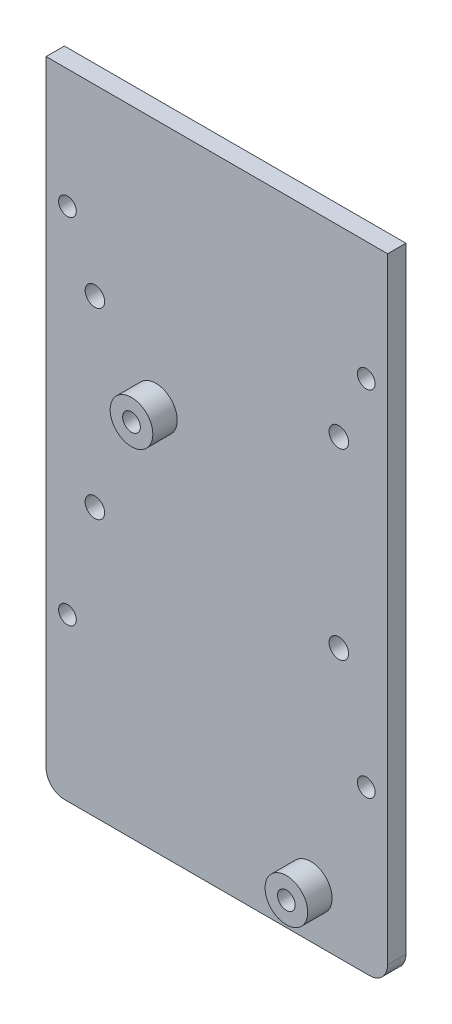
SolidWorks part; units mm, degrees
material "ABS"
ref_plane "Front Plane" through (0, 0, 0) normal (0, 0, 1) x (1, 0, 0)
ref_plane "Top Plane" through (0, 0, 0) normal (0, 1, 0) x (1, 0, 0)
ref_plane "Right Plane" through (0, 0, 0) normal (1, 0, 0) x (0, 0, -1)
sketch "Sketch2" plane through (0, 0, 0) normal (0, 0, 1) x (1, 0, 0)
  line L0 (-15.1668, -33.2317) -> (-15.1668, -38.1317) construction
  line L1 (-15.1668, -33.2317) -> (-2.5668, -33.2317) construction
  line L2 (-40.5668, 21.9683) -> (-40.5668, -38.1317) construction
  line L3 (-40.5668, 21.9683) -> (-2.5668, 21.9683) construction
  line L4 (-55.5668, -38.1317) -> (-5.5668, -38.1317)
  line L5 (-2.5668, -35.1317) -> (-2.5668, 65.8683)
  line L6 (-58.5668, 65.8683) -> (-58.5668, -35.1317)
  line L7 (-55.5668, -38.1317) -> (-5.5668, -38.1317) construction
  line L8 (-2.5668, -35.1317) -> (-2.5668, 65.8683) construction
  line L9 (-2.5668, 65.8683) -> (-58.5668, 65.8683)
  line L10 (-58.5668, 65.8683) -> (-58.5668, -35.1317) construction
  line L11 (-30.5668, -38.1317) -> (-30.5668, 46.8683) construction
  line L12 (-58.5668, 46.8683) -> (-2.5668, 46.8683) construction
  line L13 (-30.5668, 65.8683) -> (-30.5668, 10.8683) construction
  line L14 (-30.5668, 10.8683) -> (-2.5668, 10.8683) construction
  arc A1 (-5.5668, -38.1317) -> (-2.5668, -35.1317) centre (-5.5668, -35.1317) ccw
  arc A2 (-58.5668, -35.1317) -> (-55.5668, -38.1317) centre (-55.5668, -35.1317) ccw
  circle A3 centre (-15.1668, -33.2317) radius 1.25 construction
  circle A4 centre (-40.5668, 21.9683) radius 1.25 construction
  arc A5 (-5.5668, -38.1317) -> (-2.5668, -35.1317) centre (-5.5668, -35.1317) ccw construction
  arc A6 (-58.5668, -35.1317) -> (-55.5668, -38.1317) centre (-55.5668, -35.1317) ccw construction
extrude "Boss-Extrude1" add sketch "Sketch2" along normal blind 3
sketch "Sketch3" plane through (0, 0, 3) normal (0, 0, 1) x (1, 0, 0)
  line L0 (-30.5668, 65.8683) -> (-50.5668, 65.8683) construction
  line L1 (-2.5668, 65.8683) -> (-58.5668, 65.8683) construction
  line L2 (-50.5668, 65.8683) -> (-50.5668, 35.8683) construction
  line L3 (-2.5668, 47.3683) -> (-2.5668, 43.8683) construction
  line L4 (-50.5668, 35.8683) -> (-50.5668, 5.8683) construction
  line L5 (-30.5668, 65.8683) -> (-30.5668, 46.8683) construction
  line L7 (-2.5668, 43.8683) -> (-6.0668, 43.8683) construction
  line L8 (-6.0668, 43.8683) -> (-6.0668, -14.1317) construction
  line L9 (-6.0668, -14.1317) -> (-6.0668, -37.6317) construction
  line L11 (-55.0668, 46.3683) -> (-58.5668, 46.3683) construction
  line L12 (-58.5668, 65.8683) -> (-58.5668, -35.1317) construction
  line L13 (-55.0668, -11.6317) -> (-58.5668, -11.6317) construction
  circle A0 centre (-50.5668, 35.8683) radius 1.6
  circle A1 centre (-50.5668, 5.8683) radius 1.6
  circle A2 centre (-10.5668, 5.8683) radius 1.6
  circle A3 centre (-10.5668, 35.8683) radius 1.6
  circle A4 centre (-40.5668, 24.9683) radius 1.45
  circle A5 centre (-15.1668, -30.2317) radius 1.45
  circle A6 centre (-6.0668, 46.3683) radius 1.45
  circle A7 centre (-6.0668, -11.6317) radius 1.45
  circle A8 centre (-55.0668, -11.6317) radius 1.45
  circle A9 centre (-55.0668, 46.3683) radius 1.45
extrude "Cut-Extrude1" cut sketch "Sketch3" against normal through all
sketch "Sketch4" plane through (0, 0, 3) normal (0, 0, 1) x (1, 0, 0)
  line L4 (-55.5668, -38.1317) -> (-5.5668, -38.1317)
  line L5 (-2.5668, -35.1317) -> (-2.5668, 65.8683)
  line L6 (-2.5668, 65.8683) -> (-58.5668, 65.8683)
  line L7 (-58.5668, 65.8683) -> (-58.5668, -35.1317)
  line L8 (-55.5668, -38.1317) -> (-5.5668, -38.1317)
  line L9 (-2.5668, -35.1317) -> (-2.5668, 65.8683)
  line L10 (-2.5668, 65.8683) -> (-58.5668, 65.8683)
  line L11 (-58.5668, 65.8683) -> (-58.5668, -35.1317)
  circle A0 centre (-55.0668, 46.3683) radius 1.45 construction
  circle A1 centre (-55.0668, -11.6317) radius 1.45 construction
  arc A2 (-58.5668, -35.1317) -> (-55.5668, -38.1317) centre (-55.5668, -35.1317) ccw
  arc A3 (-5.5668, -38.1317) -> (-2.5668, -35.1317) centre (-5.5668, -35.1317) ccw
  arc A4 (-58.5668, -35.1317) -> (-55.5668, -38.1317) centre (-55.5668, -35.1317) ccw
  arc A5 (-5.5668, -38.1317) -> (-2.5668, -35.1317) centre (-5.5668, -35.1317) ccw
  circle A6 centre (-6.0668, 46.3683) radius 1.45 construction
  circle A8 centre (-6.0668, -11.6317) radius 1.45 construction
  circle A10 centre (-55.0668, 46.3683) radius 1.45
  circle A11 centre (-55.0668, -11.6317) radius 1.45
  circle A12 centre (-6.0668, 46.3683) radius 1.45
  circle A13 centre (-40.5668, 24.9683) radius 1.45
  circle A14 centre (-6.0668, -11.6317) radius 1.45
  circle A15 centre (-15.1668, -30.2317) radius 1.25
  circle A16 centre (-55.0668, 46.3683) radius 3.6293
  circle A17 centre (-40.5668, 24.9683) radius 3.5
  circle A18 centre (-55.0668, -11.6317) radius 3.6293
  circle A19 centre (-15.1668, -30.2317) radius 3.5
  circle A20 centre (-6.0668, -11.6317) radius 3.6293
  circle A21 centre (-6.0668, 46.3683) radius 3.6293
  circle M12 centre (-40.5668, 24.9683) radius 1.45
  dimension "D1" = 0
extrude "Boss-Extrude2" add sketch "Sketch4" along normal blind 4 contours A19 A15 | A17 M12 | A16
